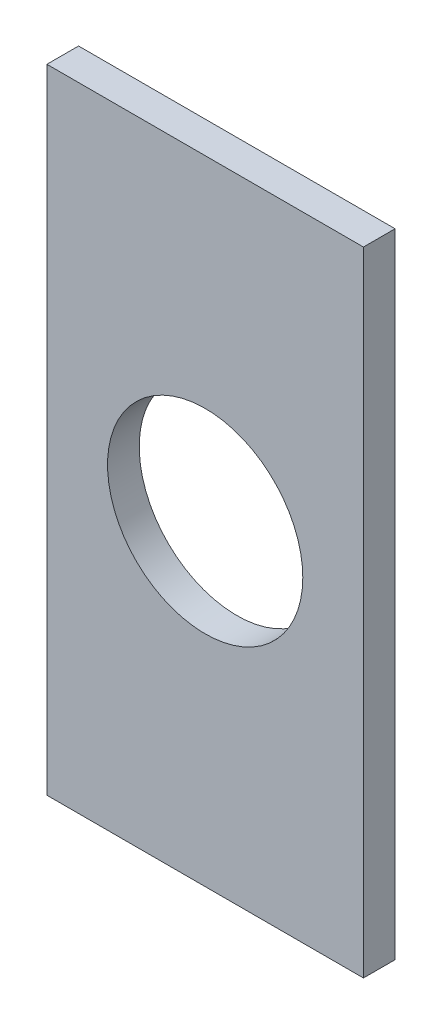
SolidWorks part; units mm, degrees
ref_plane "Front Plane" through (0, 0, 0) normal (0, 0, 1) x (1, 0, 0)
ref_plane "Top Plane" through (0, 0, 0) normal (0, 1, 0) x (1, 0, 0)
ref_plane "Right Plane" through (0, 0, 0) normal (1, 0, 0) x (0, 0, -1)
sketch "Sketch1" plane through (0, 0, 0) normal (0, 0, 1) x (1, 0, 0)
  line L1 (-25, 50) -> (25, 50)
  line L2 (-25, 50) -> (-25, -50)
  line L3 (-25, -50) -> (25, -50)
  line L4 (25, 50) -> (25, -50)
  line L5 (-25, 50) -> (25, -50) construction
  line L6 (-25, -50) -> (25, 50) construction
  point P0 (0, 0)
  dimension "D1" = 50
  dimension "D2" = 100
extrude "Boss-Extrude1" add sketch "Sketch1" along normal blind 5
sketch "Sketch2" plane through (0, 0, 5) normal (0, 0, 1) x (1, 0, 0)
  circle A0 centre (0, 0) radius 15.4211
extrude "Cut-Extrude1" cut sketch "Sketch2" against normal blind 5
